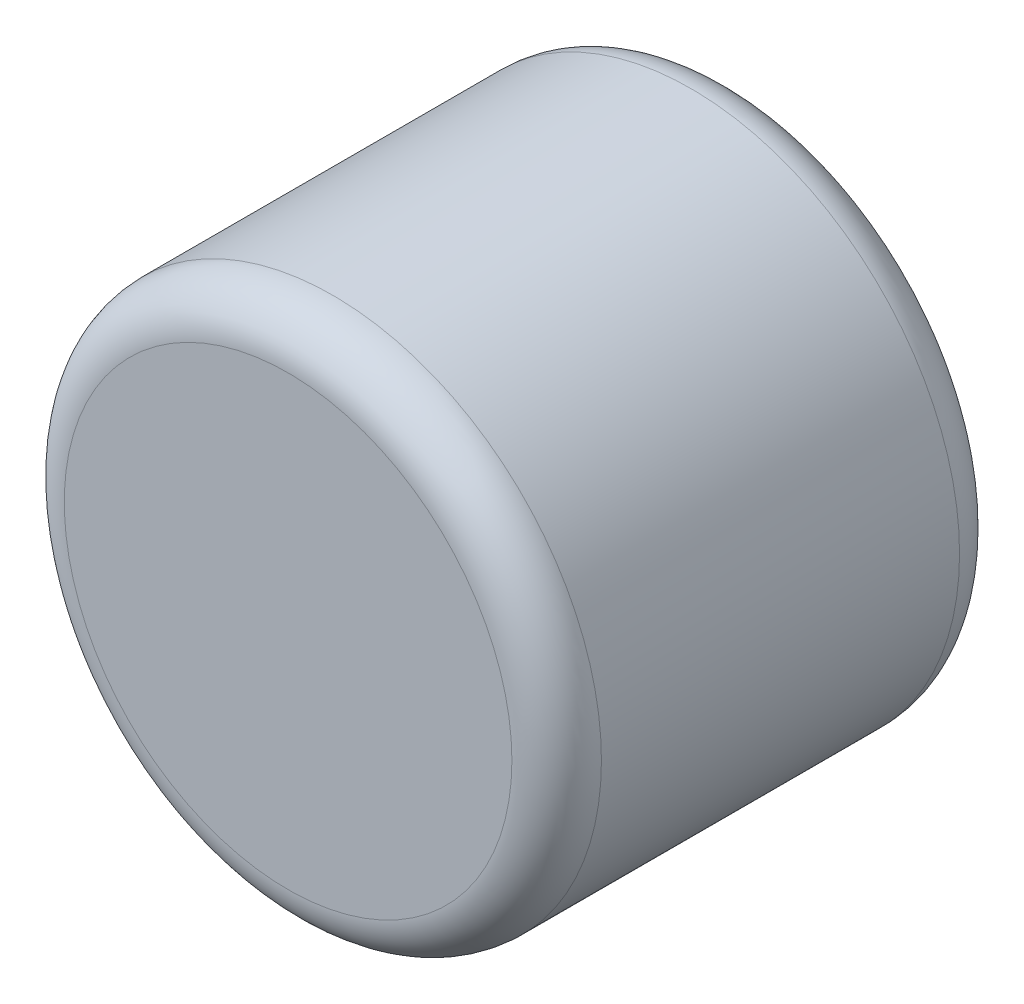
SolidWorks part; units mm, degrees
ref_plane "Front Plane" through (0, 0, 0) normal (0, 0, 1) x (1, 0, 0)
ref_plane "Top Plane" through (0, 0, 0) normal (0, 1, 0) x (1, 0, 0)
ref_plane "Right Plane" through (0, 0, 0) normal (1, 0, 0) x (0, 0, -1)
sketch "Sketch1" plane through (0, 0, 0) normal (0, 0, 1) x (1, 0, 0)
  circle A0 centre (0, 0) radius 76.2
extrude "Boss-Extrude1" add sketch "Sketch1" along normal blind 127
fillet "Fillet1" radius 12.7 2 edges at (76.2, 0, 0) (76.2, 0, 127)
